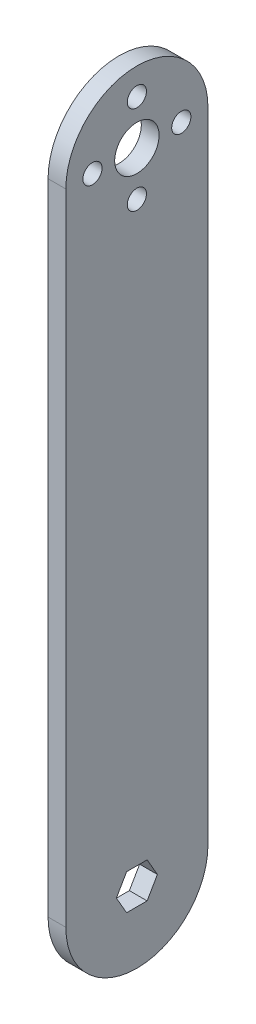
SolidWorks part; units mm, degrees
ref_plane "Front Plane" through (0, 0, 0) normal (0, 0, 1) x (1, 0, 0)
ref_plane "Top Plane" through (0, 0, 0) normal (0, 1, 0) x (1, 0, 0)
ref_plane "Right Plane" through (0, 0, 0) normal (1, 0, 0) x (0, 0, -1)
sketch "Sketch1" plane through (0, 0, 0) normal (1, 0, 0) x (0, 0, -1)
  line L0 (0, 0) -> (0, 228.6) construction
  line L1 (7.3323, 0) -> (3.6662, 6.35)
  line L2 (3.6662, 6.35) -> (-3.6662, 6.35)
  line L3 (-3.6662, 6.35) -> (-7.3323, 0)
  line L4 (-7.3323, 0) -> (-3.6662, -6.35)
  line L5 (-3.6662, -6.35) -> (3.6662, -6.35)
  line L6 (3.6662, -6.35) -> (7.3323, 0)
  line L7 (0, 55) -> (0, -55) construction
  line L8 (0, 228.6) -> (0, 212.725) construction
  line L9 (-25.4, 228.6) -> (-25.4, 0)
  line L10 (25.4, 228.6) -> (25.4, 0)
  circle A0 centre (0, 0) radius 6.35 construction
  circle A1 centre (0, 228.6) radius 7.9375
  circle A2 centre (0, 228.6) radius 15.875 construction
  circle A3 centre (0, 212.725) radius 3.429
  circle A4 centre (-15.875, 228.6) radius 3.429
  circle A5 centre (0, 244.475) radius 3.429
  circle A6 centre (15.875, 228.6) radius 3.429
  arc A7 (25.4, 228.6) -> (-25.4, 228.6) centre (0, 228.6) ccw
  arc A8 (-25.4, 0) -> (25.4, 0) centre (0, 0) ccw
  dimension "D1" = 12.7
  dimension "D3" = 15.875
  dimension "D4" = 31.75
  dimension "D5" = 6.858
  dimension "D8" = 25.4
  dimension "D2" = 228.6
  dimension "D7" = 15.875
  dimension "D6" = 4
extrude "Boss-Extrude1" add sketch "Sketch1" along normal blind 6.35
